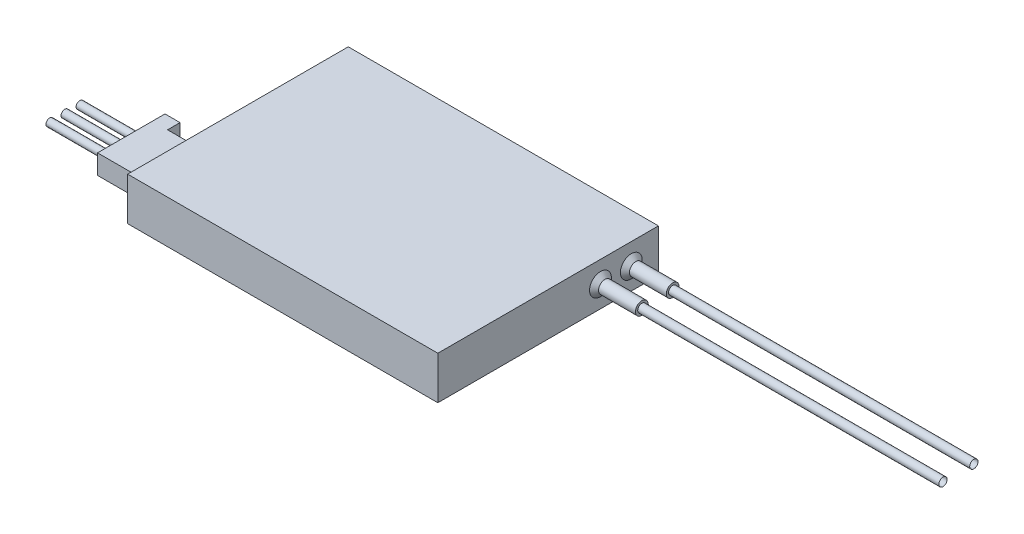
SolidWorks part; units mm, degrees
ref_plane "前视基准面" through (0, 0, 0) normal (0, 0, 1) x (1, 0, 0)
ref_plane "上视基准面" through (0, 0, 0) normal (0, 1, 0) x (1, 0, 0)
ref_plane "右视基准面" through (0, 0, 0) normal (1, 0, 0) x (0, 0, -1)
sketch "草图1" plane through (0, 0, 0) normal (0, 1, 0) x (1, 0, 0)
  line L1 (-20.6, 14.65) -> (20.6, 14.65)
  line L2 (-20.6, 14.65) -> (-20.6, -14.65)
  line L3 (-20.6, -14.65) -> (20.6, -14.65)
  line L4 (20.6, 14.65) -> (20.6, -14.65)
  line L5 (0, -14.65) -> (0, 14.65) construction
  line L6 (-20.6, 0) -> (20.6, 0) construction
  point P0 (0, 0)
  dimension "D1" = 29.3
  dimension "D2" = 41.2
extrude "凸台-拉伸1" add sketch "草图1" along normal blind 5.7
sketch "草图2" plane through (20.6, 0, 0) normal (1, 0, 0) x (0, 0, -1)
  line L0 (14.65, 5.7) -> (14.65, 0) construction
  line L1 (6.95, 2.85) -> (11.05, 2.85) construction
  line L2 (11.05, 2.85) -> (14.65, 2.85) construction
  circle A0 centre (11.05, 2.85) radius 0.85
  circle A1 centre (6.95, 2.85) radius 0.85
  dimension "D1" = 7.7
  dimension "D2" = 3.6
  dimension "D3" = 1.7
  dimension "D4" = 1.7
extrude "凸台-拉伸2" add sketch "草图2" along normal blind 5.5
chamfer "倒角1" distance 0.6 angle 45 2 edges at (20.6, 2.85, -10.2) (20.6, 2.85, -6.1)
sketch "草图3" plane through (26.1, 0, 0) normal (1, 0, 0) x (0, 0, -1)
  circle A0 centre (6.95, 2.85) radius 0.55
  circle A1 centre (11.05, 2.85) radius 0.55
  dimension "D1" = 1.1
  dimension "D2" = 1.1
surface "曲面-拉伸1" sketch "草图3" parameters "D1"=40
sketch "草图4" plane through (-20.6, 0, 0) normal (-1, 0, 0) x (0, 0, 1)
  line L0 (14.65, 5.7) -> (14.65, 0) construction
  line L1 (5.35, 4.15) -> (12.65, 4.15)
  line L2 (5.35, 4.15) -> (5.35, 1.55)
  line L3 (5.35, 1.55) -> (12.65, 1.55)
  line L4 (12.65, 4.15) -> (12.65, 1.55)
  line L5 (9, 1.55) -> (9, 4.15) construction
  line L6 (5.35, 2.85) -> (12.65, 2.85) construction
  line L7 (12.65, 2.85) -> (14.65, 2.85) construction
  point P0 (9, 2.85)
  dimension "D1" = 9.3
  dimension "D2" = 2
  dimension "D3" = 2.6
extrude "凸台-拉伸3" add sketch "草图4" along normal blind 6
sketch "草图5" plane through (-26.6, 0, 0) normal (-1, 0, 0) x (0, 0, 1)
  line L1 (5.35, 4.15) -> (3.6915, 4.15)
  line L2 (5.35, 4.15) -> (5.35, 1.55)
  line L3 (5.35, 1.55) -> (3.6915, 1.55)
  line L4 (3.6915, 4.15) -> (3.6915, 1.55)
extrude "凸台-拉伸4" add sketch "草图5" against normal blind 2
sketch "草图6" plane through (-26.6, 0, 0) normal (-1, 0, 0) x (0, 0, 1)
  line L0 (5.35, 4.15) -> (5.35, 1.55) construction
  line L1 (5.35, 4.15) -> (5.35, 1.55) construction
  line L2 (5.35, 2.85) -> (7, 2.85) construction
  line L3 (7, 2.85) -> (9, 2.85) construction
  line L4 (9, 1.55) -> (9, 2.85) construction
  line L5 (11.3567, 2.85) -> (9, 2.85) construction
  line L6 (5.35, 1.55) -> (12.65, 1.55) construction
  circle A0 centre (7, 2.85) radius 0.4985
  circle A1 centre (9, 2.85) radius 0.4985
  circle A3 centre (11, 2.85) radius 0.4985
  dimension "D1" = 0.9971
  dimension "D2" = 4
extrude "凸台-拉伸5" add sketch "草图6" along normal blind 8
sketch "草图7" plane through (0, 0, 0) normal (0, -1, 0) x (1, 0, 0)
  line L0 (-1.4, -10.65) -> (-1.4, 6.0853) construction
  line L1 (20.6, 14.65) -> (20.6, -14.65) construction
  line L2 (20.6, -14.65) -> (-20.6, -14.65) construction
  line L3 (-5.9, -10.65) -> (-5.9, 6.9907) construction
  line L4 (-5.9, -10.65) -> (-1.4, -10.65) construction
  line L5 (-8.6045, 0) -> (-20.6, 0) construction
  line L6 (-8.6045, -10.65) -> (-8.4045, -10.65)
  line L7 (-8.6045, -10.65) -> (-8.6045, 10.65)
  line L8 (-8.6045, 10.65) -> (-8.4045, 10.65)
  line L9 (-8.4045, -10.65) -> (-8.4045, 10.65)
  line L10 (-20.6, -14.65) -> (-20.6, 14.65) construction
  line L11 (-5.9, -10.65) -> (-8.4045, -10.65) construction
  line L12 (-9.2011, -10.65) -> (-9.2011, 1.2986) construction
  text T0 "DR16" font "黑体" height 3.5
  text T2 "DESST" font "黑体" height 2
  dimension "D1" = 22
  dimension "D2" = 4
  dimension "D3" = 26.5
  dimension "D4" = 0.2
extrude "切除-拉伸1" cut sketch "草图7" against normal blind 0.01
sketch "草图8" plane through (0, 0, 0) normal (0, -1, 0) x (1, 0, 0)
  line L0 (-5.9, -10.65) -> (-5.9, 11.4564) construction
  line L1 (20.6, 14.65) -> (20.6, -14.65) construction
  line L2 (-5.9, -10.65) -> (-8.4045, -10.65) construction
  text T0 "DJI RECEIVER" font "黑体" height 2
  dimension "D1" = 26.5
extrude "切除-拉伸2" cut sketch "草图8" against normal blind 0.01
